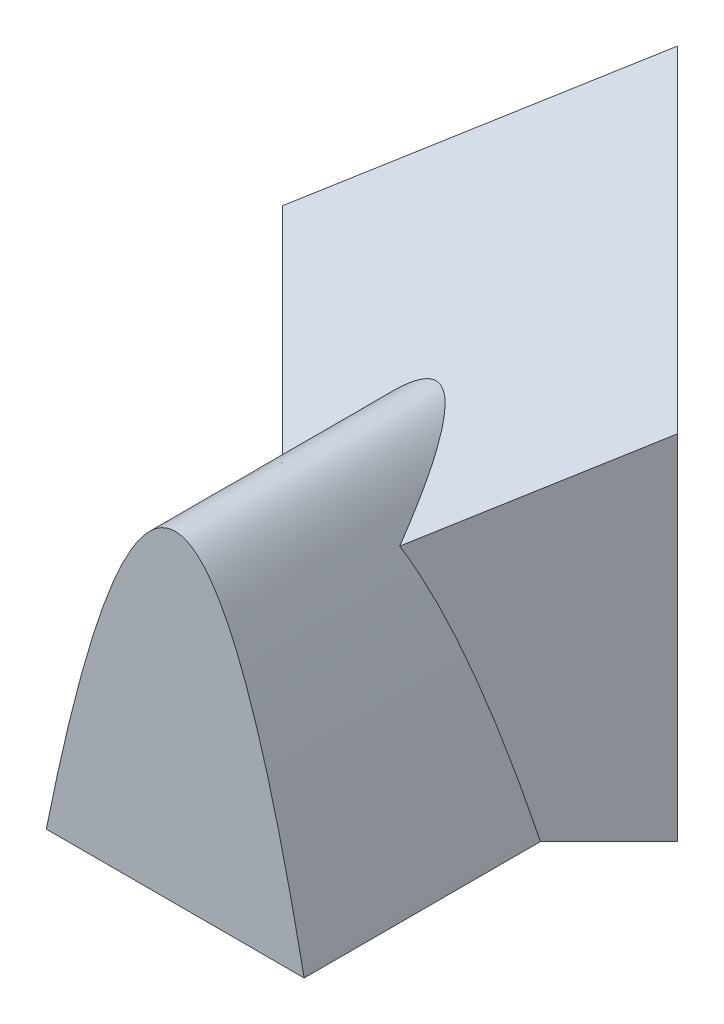
SolidWorks part; units mm, degrees
ref_plane "Front" through (0, 0, 0) normal (0, 0, 1) x (1, 0, 0)
ref_plane "Top" through (0, 0, 0) normal (0, 1, 0) x (1, 0, 0)
ref_plane "Right" through (0, 0, 0) normal (1, 0, 0) x (0, 0, -1)
sketch "Sketch1" plane through (0, 0, 0) normal (0, 1, 0) x (1, 0, 0)
  line L0 (0, 0) -> (91.9239, 91.9239)
  line L1 (91.9239, 91.9239) -> (0, 183.8478)
  line L2 (0, 183.8478) -> (-91.9239, 91.9239)
  line L3 (-91.9239, 91.9239) -> (0, 0)
  dimension "D1" = 130
extrude "Extrude1" add sketch "Sketch1" along normal blind 228.73
sketch "Sketch2" plane through (0, 0, 0) normal (1, 0, 0) x (0, 0, -1)
  line L0 (183.8478, 100) -> (0, 100) construction
  line L1 (183.8478, 228.73) -> (183.8478, 0) construction
  line L2 (0, 228.73) -> (0, 0) construction
  line L3 (0, 100) -> (183.8478, 228.7316)
  line L4 (183.8478, 0) -> (91.9239, 0) construction
  line L6 (183.8478, 228.7316) -> (0, 228.7316)
  line L7 (0, 228.7316) -> (0, 100)
  dimension "D1" = 100
  dimension "D2" = 35
extrude "Cut-Extrude1" cut sketch "Sketch2" against normal mid plane 190
sketch "Sketch3" plane through (0, 0, 0) normal (0, 0, 1) x (1, 0, 0)
  line L0 (0, 0) -> (0, 150) construction
  line L1 (60, 0) -> (60, 150) construction
  line L2 (-60, 0) -> (-60, 150) construction
  line L3 (-60, 0) -> (-60, 228.2217) construction
  line L4 (-60, 150) -> (60, 150) construction
  line L5 (-91.9239, 0) -> (0, 0) construction
  line L6 (0, 0) -> (0, 228.2217) construction
  line L7 (60, 0) -> (60, 228.2217) construction
  line L8 (-60, 0) -> (60, 0)
  parabola Q0 (-60, 0) -> (60, 0) focus (0, 144) apex (0, 150)
  dimension "D1" = 150
  dimension "D2" = 60
extrude "Extrude2" add sketch "Sketch3" along normal blind 50 and the other way blind 100
